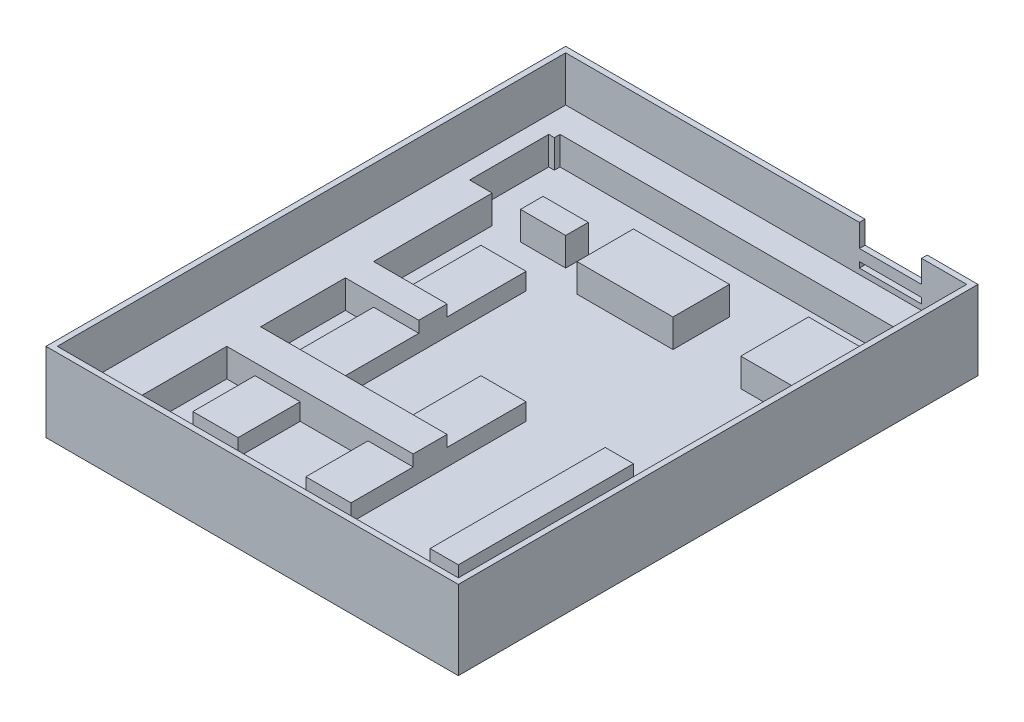
SolidWorks part; units mm, degrees
ref_plane "前视基准面" through (0, 0, 0) normal (0, 0, 1) x (1, 0, 0)
ref_plane "上视基准面" through (0, 0, 0) normal (0, 1, 0) x (1, 0, 0)
ref_plane "右视基准面" through (0, 0, 0) normal (1, 0, 0) x (0, 0, -1)
sketch "草图8" plane through (0, 0, 0) normal (0, 1, 0) x (1, 0, 0)
  line L1 (0, 0) -> (73, 0)
  line L2 (0, 0) -> (0, 92)
  line L3 (0, 92) -> (73, 92)
  line L4 (73, 0) -> (73, 92)
  dimension "D1" = 92
  dimension "D2" = 73
extrude "凸台-拉伸5" add sketch "草图8" along normal blind 12
sketch "草图9" plane through (0, 12, 0) normal (0, 1, 0) x (1, 0, 0)
  line L0 (73, 92) -> (0, 92) construction
  line L1 (1, 91) -> (72, 91)
  line L2 (1, 91) -> (1, 1)
  line L3 (1, 1) -> (72, 1)
  line L4 (72, 91) -> (72, 1)
  line L5 (0, 92) -> (0, 0) construction
  line L6 (73, 0) -> (73, 92) construction
  line L7 (0, 0) -> (73, 0) construction
  point P4 (1, 86.807)
  point P5 (72, 84.7205)
  point P6 (0, 86.807)
  point P7 (73, 84.7205)
  point P14 (15.1418, 92)
  point P15 (15.1418, 91)
  point P16 (27.8731, 1)
  point P17 (27.8731, 0)
  dimension "D1" = 71
  dimension "D2" = 90
  dimension "D3" = 1
  dimension "D4" = 1
  dimension "D5" = 1
  dimension "D6" = 1
extrude "切除-拉伸3" cut sketch "草图9" against normal blind 10
sketch "草图11" plane through (0, 0, 0) normal (0, 1, 0) x (1, 0, 0)
  line L0 (73, 0) -> (73, 92) construction
  line L1 (0, 92) -> (73, 92)
  line L2 (0, 92) -> (0, 86)
  line L3 (0, 86) -> (73, 86)
  line L4 (73, 92) -> (73, 86)
  dimension "D1" = 6
extrude "凸台-拉伸8" add sketch "草图11" along normal blind 7
sketch "草图12" plane through (0, 0, 0) normal (0, 1, 0) x (1, 0, 0)
  line L0 (73, 92) -> (0, 92) construction
  line L1 (69, 92) -> (73, 92)
  line L2 (69, 92) -> (69, 73)
  line L3 (69, 73) -> (73, 73)
  line L4 (73, 92) -> (73, 73)
  line L5 (73, 0) -> (73, 92) construction
  dimension "D1" = 4
  dimension "D2" = 19
extrude "凸台-拉伸10" add sketch "草图12" along normal blind 7
sketch "草图13" plane through (0, 0, 0) normal (0, 1, 0) x (1, 0, 0)
  line L1 (0, 92) -> (4, 92)
  line L2 (0, 92) -> (0, 71)
  line L3 (0, 71) -> (4, 71)
  line L4 (4, 92) -> (4, 71)
  dimension "D1" = 21
  dimension "D2" = 4
extrude "凸台-拉伸13" add sketch "草图13" along normal blind 7
sketch "草图14" plane through (0, 0, 0) normal (0, 1, 0) x (1, 0, 0)
  line L1 (1, 71) -> (8, 71)
  line L2 (1, 71) -> (1, 59)
  line L3 (1, 59) -> (8, 59)
  line L4 (8, 71) -> (8, 59)
  dimension "D1" = 12
  dimension "D2" = 7
extrude "凸台-拉伸14" add sketch "草图14" along normal blind 7
sketch "草图15" plane through (0, 0, 0) normal (0, 1, 0) x (1, 0, 0)
  line L0 (1, 1) -> (72, 1) construction
  line L1 (1, 59) -> (8, 59)
  line L2 (1, 59) -> (1, 1)
  line L3 (1, 1) -> (8, 1)
  line L4 (8, 59) -> (8, 1)
  dimension "D1" = 7
extrude "凸台-拉伸15" add sketch "草图15" along normal blind 7
ref_plane "基准面9" through (8, 2, -1) normal (0, 0, 1) x (1, 0, 0)
sketch "草图17" plane through (0, 0, 0) normal (0, 1, 0) x (1, 0, 0)
  line L0 (8, 1) -> (8, 71) construction
  line L1 (-11.25, 1) -> (27.25, 1) construction
  line L2 (1, 91) -> (1, 1) construction
  line L3 (1, 30) -> (41, 30)
  line L4 (1, 30) -> (1, 24)
  line L5 (1, 24) -> (41, 24)
  line L6 (41, 30) -> (41, 24)
  point P0 (8, 24)
  point P5 (8, 30)
  dimension "D1" = 23
  dimension "D2" = 29
  dimension "D3" = 40
extrude "凸台-拉伸16" add sketch "草图17" along normal blind 7
sketch "草图18" plane through (0, 0, 0) normal (0, 1, 0) x (1, 0, 0)
  line L0 (1, 91) -> (1, 1) construction
  line L1 (-11.25, 1) -> (27.25, 1) construction
  line L2 (1, 1) -> (1, 91) construction
  line L4 (1, 50) -> (21, 50)
  line L5 (1, 50) -> (1, 45)
  line L6 (1, 45) -> (21, 45)
  line L7 (21, 50) -> (21, 45)
  point P0 (1, 45)
  point P5 (1, 50)
  dimension "D1" = 44
  dimension "D2" = 49
  dimension "D3" = 20
extrude "凸台-拉伸17" add sketch "草图18" along normal blind 7
sketch "草图19" plane through (0, 0, 0) normal (0, 1, 0) x (1, 0, 0)
  line L1 (72, 1) -> (56, 1)
  line L2 (72, 1) -> (72, 5)
  line L3 (72, 5) -> (56, 5)
  line L4 (56, 1) -> (56, 5)
  dimension "D1" = 4
  dimension "D2" = 16
extrude "凸台-拉伸18" add sketch "草图19" along normal blind 7
sketch "草图20" plane through (0, 0, 0) normal (0, 1, 0) x (1, 0, 0)
  line L1 (72, 1) -> (68, 1)
  line L2 (72, 1) -> (72, 8)
  line L3 (72, 8) -> (68, 8)
  line L4 (68, 1) -> (68, 8)
  dimension "D1" = 4
  dimension "D2" = 7
extrude "凸台-拉伸19" add sketch "草图20" along normal blind 7
sketch "草图21" plane through (0, 0, 0) normal (0, 1, 0) x (1, 0, 0)
  line L0 (72, 8) -> (72, 73) construction
  line L2 (56, 1) -> (72, 1) construction
  line L3 (60, 44) -> (55, 44)
  line L4 (60, 44) -> (60, 13)
  line L5 (60, 13) -> (55, 13)
  line L6 (55, 44) -> (55, 13)
  point P0 (72, 12.9999)
  point P1 (72, 64)
  point P4 (60, 1)
  dimension "D1" = 12
  dimension "D2" = 12
  dimension "D3" = 43
  dimension "D4" = 5
extrude "凸台-拉伸22" add sketch "草图21" along normal blind 5
sketch "草图23" plane through (0, 0, 0) normal (0, 1, 0) x (1, 0, 0)
  line L0 (72, 91) -> (72, 73) construction
  line L1 (72, 8) -> (72, 73) construction
  line L2 (1, 91) -> (72, 91) construction
  line L3 (72, 91) -> (1, 91) construction
  line L5 (64, 80) -> (55, 80)
  line L6 (64, 80) -> (64, 68)
  line L7 (64, 68) -> (55, 68)
  line L8 (55, 80) -> (55, 68)
  point P0 (72, 80)
  point P1 (72, 68)
  point P5 (64, 91)
  point P9 (55, 91)
  dimension "D1" = 11
  dimension "D2" = 23
  dimension "D3" = 8
  dimension "D4" = 17
extrude "凸台-拉伸23" add sketch "草图23" along normal blind 7
sketch "草图24" plane through (0, 0, 0) normal (0, 1, 0) x (1, 0, 0)
  line L0 (1, 1) -> (1, 91) construction
  line L1 (72, 91) -> (1, 91) construction
  line L3 (26, 78) -> (43, 78)
  line L4 (26, 78) -> (26, 68)
  line L5 (26, 68) -> (43, 68)
  line L6 (43, 78) -> (43, 68)
  point P0 (1, 78)
  point P1 (1, 68)
  point P5 (26, 91)
  point P6 (43, 91)
  dimension "D1" = 13
  dimension "D2" = 23
  dimension "D3" = 25
  dimension "D4" = 42
extrude "凸台-拉伸24" add sketch "草图24" along normal blind 7
sketch "草图25" plane through (0, 0, 0) normal (0, 1, 0) x (1, 0, 0)
  line L0 (1, 91) -> (1, 1) construction
  line L1 (1, 1) -> (1, 91) construction
  line L2 (1, 91) -> (72, 91) construction
  line L4 (13, 75) -> (21, 75)
  line L5 (13, 75) -> (13, 71)
  line L6 (13, 71) -> (21, 71)
  line L7 (21, 75) -> (21, 71)
  point P0 (1, 75)
  point P1 (1, 71)
  point P5 (13, 91)
  point P8 (21, 91)
  dimension "D1" = 16
  dimension "D2" = 20
  dimension "D3" = 12
  dimension "D4" = 20
extrude "凸台-拉伸25" add sketch "草图25" along normal blind 7
sketch "草图28" plane through (0, 0, 0) normal (0, 1, 0) x (1, 0, 0)
  line L0 (8, 1) -> (56, 1) construction
  line L1 (1, 1) -> (72, 1) construction
  line L2 (1, 1) -> (1, 91) construction
  line L4 (33, 44) -> (41, 44)
  line L5 (33, 44) -> (33, 13)
  line L6 (33, 13) -> (41, 13)
  line L7 (41, 44) -> (41, 13)
  point P0 (33, 1)
  point P1 (41, 1)
  point P5 (1, 13)
  point P9 (1, 44)
  dimension "D1" = 32
  dimension "D2" = 40
  dimension "D3" = 12
  dimension "D4" = 43
extrude "凸台-拉伸26" add sketch "草图28" along normal blind 5
ref_plane "基准面11" through (0, 12, 0) normal (0, 1, 0) x (1, 0, 0)
sketch "草图32" plane through (0, 12, 0) normal (0, 1, 0) x (1, 0, 0)
  line L0 (72, 91) -> (1, 91) construction
  line L1 (1, 91) -> (72, 91) construction
  line L2 (73, 92) -> (0, 92) construction
  line L3 (53, 91) -> (63, 91)
  line L4 (53, 91) -> (53, 92)
  line L5 (53, 92) -> (63, 92)
  line L6 (63, 91) -> (63, 92)
  point P0 (63, 91)
  point P1 (53, 91)
  dimension "D1" = 9
  dimension "D2" = 10
extrude "切除-拉伸4" cut sketch "草图32" against normal blind 5
sketch "草图33" plane through (0, 0, 0) normal (0, 1, 0) x (1, 0, 0)
  line L0 (1, 1) -> (1, 91) construction
  line L1 (8, 1) -> (56, 1) construction
  line L3 (13, 64) -> (21, 64)
  line L4 (13, 64) -> (13, 13)
  line L5 (13, 13) -> (21, 13)
  line L6 (21, 64) -> (21, 13)
  point P0 (1, 13)
  point P1 (13, 1)
  point P5 (21, 1)
  point P8 (1, 64)
  dimension "D1" = 12
  dimension "D2" = 12
  dimension "D3" = 20
  dimension "D4" = 63
extrude "凸台-拉伸27" add sketch "草图33" along normal blind 5
sketch "草图35" plane through (0, 12, 0) normal (0, 1, 0) x (1, 0, 0)
  line L1 (53, 92) -> (63, 92)
  line L2 (53, 92) -> (53, 91)
  line L3 (53, 91) -> (63, 91)
  line L4 (63, 92) -> (63, 91)
extrude "凸台-拉伸28" add sketch "草图35" against normal blind 10
sketch "草图37" plane through (0, 12, 0) normal (0, 1, 0) x (1, 0, 0)
  line L0 (1, 91) -> (72, 91) construction
  line L1 (73, 92) -> (0, 92) construction
  line L2 (53, 92) -> (64, 92)
  line L3 (53, 92) -> (53, 91)
  line L4 (53, 91) -> (64, 91)
  line L5 (64, 92) -> (64, 91)
  point P0 (64, 91)
  point P1 (53, 91)
  dimension "D1" = 8
  dimension "D2" = 11
extrude "切除-拉伸7" cut sketch "草图37" against normal blind 1
ref_plane "基准面14" through (0, 8, 0) normal (0, 1, 0) x (1, 0, 0)
sketch "草图39" plane through (0, 8, 0) normal (0, 1, 0) x (1, 0, 0)
  line L1 (53, 92) -> (64, 92)
  line L2 (53, 92) -> (53, 91)
  line L3 (53, 91) -> (64, 91)
  line L4 (64, 92) -> (64, 91)
extrude "切除-拉伸8" cut sketch "草图39" along normal blind 1
sketch "草图40" plane through (0, 0, 0) normal (0, 1, 0) x (1, 0, 0)
  line L0 (4, 86) -> (4, 71) construction
  line L1 (69, 86) -> (4, 86) construction
  line L2 (4, 71) -> (4, 86) construction
  line L3 (4, 86) -> (5, 86)
  line L4 (4, 86) -> (4, 85)
  line L5 (4, 85) -> (5, 85)
  line L6 (5, 86) -> (5, 85)
  point P0 (4, 85)
  point P1 (5, 86)
  dimension "D1" = 1
  dimension "D2" = 1
extrude "凸台-拉伸29" add sketch "草图40" along normal blind 7
sketch "草图41" plane through (0, 12, 0) normal (0, 1, 0) x (1, 0, 0)
  line L0 (1, 1) -> (72, 1) construction
  line L2 (1, 91) -> (1, 1) construction
  line L3 (56, 1) -> (72, 1) construction
  line L4 (72, 1) -> (72, 8) construction
  line L5 (72, 91) -> (72, 73) construction
  line L6 (72, 91) -> (64, 91) construction
  line L7 (1, 91) -> (72, 91) construction
  circle A0 centre (4, 5) radius 1
  circle A1 centre (70, 6) radius 1
  circle A2 centre (70, 87) radius 1
  circle A3 centre (4, 87) radius 1
  point P0 (3, 1)
  point P6 (1, 4)
  point P7 (71, 1)
  point P11 (72, 4)
  point P20 (72, 88)
  point P21 (71, 91)
  point P29 (3, 91)
  point P30 (1, 88)
  dimension "D3" = 1
  dimension "D5" = 3
  dimension "D7" = 2
  dimension "D1" = 2
  dimension "D2" = 3
  dimension "D4" = 3
  dimension "D6" = 1
  dimension "D8" = 3
extrude "切除-拉伸9" cut sketch "草图41" against normal blind 9
sketch "草图42" plane through (0, 12, 0) normal (0, 1, 0) x (1, 0, 0)
  line L14 (53, 92) -> (53, 91)
  line L23 (53, 91) -> (1, 91)
  line L24 (1, 91) -> (1, 1)
  line L25 (1, 1) -> (72, 1)
  line L26 (72, 1) -> (72, 91)
  line L27 (72, 91) -> (64, 91)
  line L28 (64, 91) -> (64, 92)
  line L29 (64, 92) -> (73, 92)
  line L30 (73, 92) -> (73, 0)
  line L31 (0, 0) -> (73, 0) construction
  line L32 (73, 0) -> (73, 92) construction
  line L33 (73, 0) -> (0, 0)
  line L34 (0, 0) -> (0, 92)
  line L35 (0, 92) -> (53, 92)
extrude "凸台-拉伸30" add sketch "草图42" along normal blind 4
sketch "草图44" plane through (0, 0, 0) normal (0, 1, 0) x (1, 0, 0)
  line L0 (8, 1) -> (8, 24) construction
  line L1 (5, 85) -> (1, 85)
  line L2 (5, 85) -> (5, 91)
  line L3 (5, 91) -> (1, 91)
  line L4 (1, 85) -> (1, 91)
  line L5 (69, 86) -> (72, 86)
  line L6 (69, 86) -> (69, 91)
  line L7 (69, 91) -> (72, 91)
  line L8 (72, 86) -> (72, 91)
  line L9 (68, 8) -> (72, 8)
  line L10 (68, 8) -> (68, 1)
  line L11 (68, 1) -> (72, 1)
  line L12 (72, 8) -> (72, 1)
  line L13 (1, 1) -> (8, 1)
  line L14 (1, 1) -> (1, 8.5048)
  line L15 (1, 8.5048) -> (8, 8.5048)
  line L16 (8, 1) -> (8, 8.5048)
extrude "凸台-拉伸31" add sketch "草图44" along normal blind 7
sketch "草图45" plane through (0, 0, 0) normal (0, 0, 1) x (1, 0, 0)
  line L0 (40.15, 8) -> (-40.15, 8) construction
  line L1 (64, 9) -> (64, 8) construction
  line L2 (73, 0) -> (0, 0) construction
  line L3 (73, 16) -> (73, 0) construction
  line L5 (73, 1) -> (0, 1)
  line L6 (73, 1) -> (73, 0)
  line L7 (73, 0) -> (0, 0)
  line L8 (0, 1) -> (0, 0)
  point P0 (64, 8)
  point P1 (64, 0)
extrude "切除-拉伸10" cut sketch "草图45" against normal blind 100
sketch "草图46" plane through (0, 0, 0) normal (0, 0, 1) x (1, 0, 0)
  line L0 (73, 16) -> (64, 16) construction
  line L1 (40.15, 8) -> (-40.15, 8) construction
  point P0 (67.7275, 16)
  point P1 (67.7275, 8)
ref_plane "基准面23" through (0, 15, 0) normal (0, 1, 0) x (1, 0, 0)
sketch "草图47" plane through (0, 0, 0) normal (0, 0, 1) x (1, 0, 0)
  line L0 (40.15, 15) -> (-40.15, 15) construction
  line L1 (73, 16) -> (0, 16)
  line L2 (73, 16) -> (73, 15)
  line L3 (73, 15) -> (0, 15)
  line L4 (0, 16) -> (0, 15)
extrude "切除-拉伸11" cut sketch "草图47" against normal blind 100
